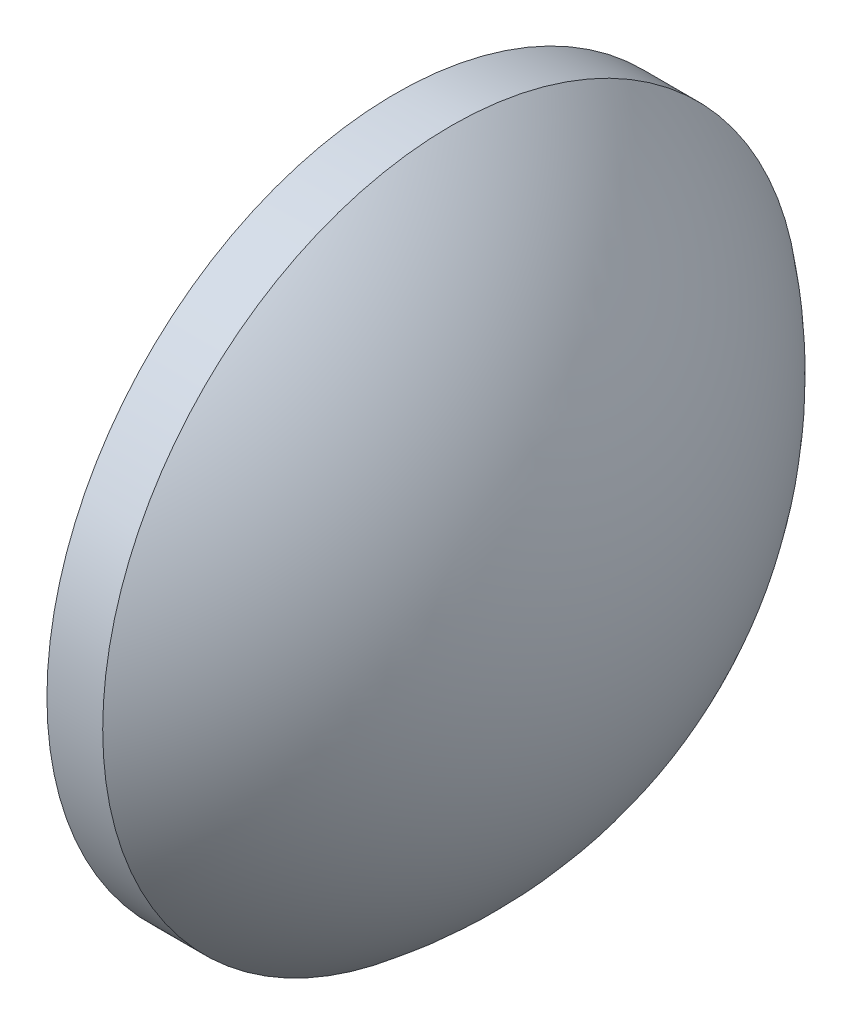
SolidWorks part; units mm, degrees
ref_plane "前视基准面" through (0, 0, 0) normal (0, 0, 1) x (1, 0, 0)
ref_plane "上视基准面" through (0, 0, 0) normal (0, 1, 0) x (1, 0, 0)
ref_plane "右视基准面" through (0, 0, 0) normal (1, 0, 0) x (0, 0, -1)
sketch "草图1" plane through (0, 0, 0) normal (0, 0, 1) x (1, 0, 0)
  line L0 (373.4601, 56.8912) -> (382.8581, 56.8912) construction
  line L1 (376.3009, 56.8912) -> (376.3009, 64.3912)
  line L2 (376.3009, 64.3912) -> (377.5009, 64.3912)
  line L3 (381.2009, 56.8912) -> (376.3009, 56.8912)
  arc A0 (381.2009, 56.8912) -> (377.5009, 64.3912) centre (371.7495, 56.8912) ccw
revolve "旋转1" add sketch "草图1" angle 360 about L0
